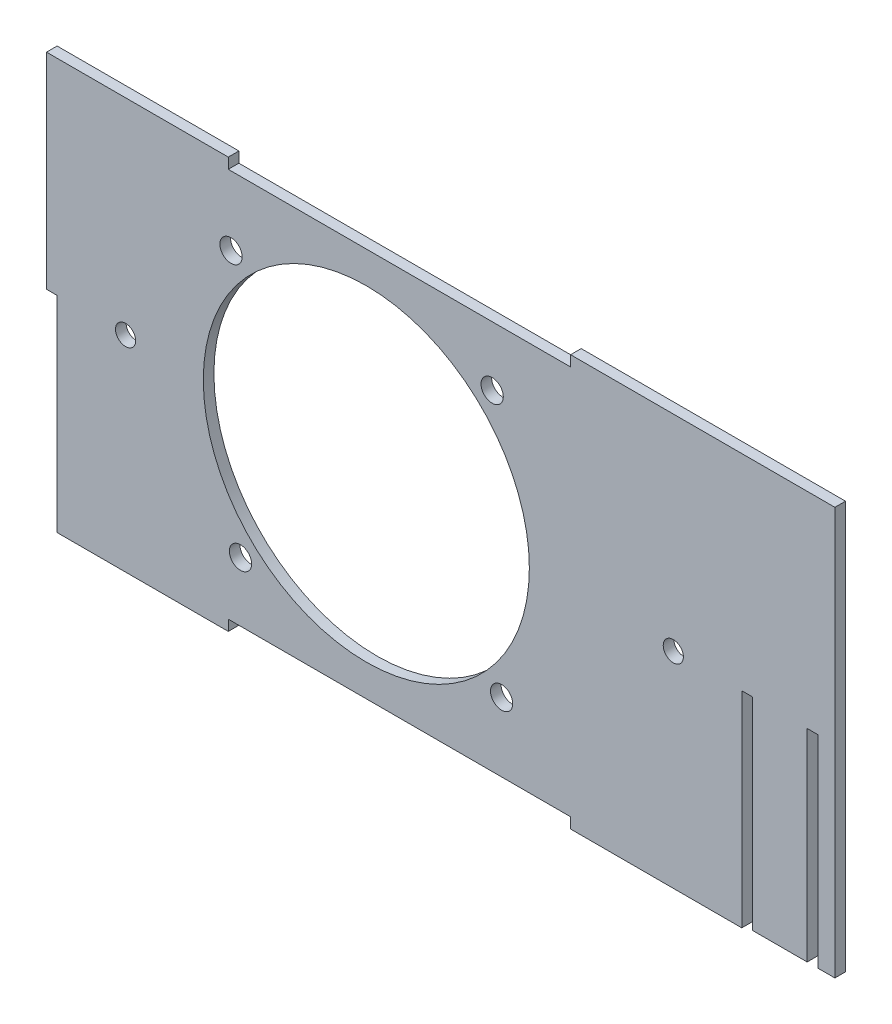
SolidWorks part; units mm, degrees
material "Teak"
ref_plane "Front Plane" through (0, 0, 0) normal (0, 0, 1) x (1, 0, 0)
ref_plane "Top Plane" through (0, 0, 0) normal (0, 1, 0) x (1, 0, 0)
ref_plane "Right Plane" through (0, 0, 0) normal (1, 0, 0) x (0, 0, -1)
sketch "Sketch1" plane through (0, 0, 0) normal (0, 0, 1) x (1, 0, 0)
  line L0 (0, 0) -> (91.2054, 0) construction
  line L1 (9.675, 0) -> (9.675, 60) construction
  line L2 (109.675, -60) -> (-90.325, -60)
  line L3 (109.675, -60) -> (109.675, 60)
  line L4 (109.675, 60) -> (-90.325, 60)
  line L5 (-90.325, -60) -> (-90.325, 60)
  line L6 (109.675, -60) -> (-90.325, 60) construction
  line L7 (109.675, 60) -> (-90.325, -60) construction
  circle A0 centre (-39.5222, 36.76) radius 3.25
  circle A1 centre (36.76, 39.5222) radius 3.25
  circle A2 centre (39.5222, -36.76) radius 3.25
  circle A3 centre (-36.76, -39.5222) radius 3.25
  circle A4 centre (0, 0) radius 47.625
  circle A5 centre (0, 0) radius 60.325 construction
  circle A6 centre (-70.325, 0) radius 2.9456
  circle A7 centre (89.675, 0) radius 2.9456
  point P3 (9.675, 0)
  point P19 (0, 0)
  dimension "D2" = 6.5
  dimension "D3" = 95.25
  dimension "D8" = 120.65
  dimension "D12" = 89.675
  dimension "D4" = 107.95
  dimension "D5" = 0
  dimension "D6" = 120
  dimension "D7" = 20
  dimension "D9" = 200
  dimension "D10" = 70.325
  dimension "D11" = 80
  dimension "D1" = 4
extrude "Boss-Extrude1" add sketch "Sketch1" along normal blind 3.1
sketch "Sketch2" plane through (0, 0, 3.1) normal (0, 0, 1) x (1, 0, 0)
  line L0 (-90.325, 0) -> (-90.325, 60)
  line L1 (-90.325, 0) -> (-93.425, 0)
  line L2 (-90.325, 60) -> (-93.425, 60)
  line L3 (-93.425, 0) -> (-93.425, 60)
  line L4 (-90.325, 60) -> (-90.325, -60) construction
  line L5 (9.675, 60) -> (9.675, -60) construction
  line L6 (109.675, 60) -> (-90.325, 60) construction
  line L7 (-90.325, -60) -> (109.675, -60) construction
  line L8 (112.775, 0) -> (112.775, 60)
  line L9 (109.675, 60) -> (112.775, 60)
  line L10 (109.675, 0) -> (112.775, 0)
  line L11 (109.675, 0) -> (109.675, 60)
  dimension "D1" = 3.1
extrude "Boss-Extrude2" add sketch "Sketch2" against normal through all
sketch "Sketch3" plane through (0, 0, 3.1) normal (0, 0, 1) x (1, 0, 0)
  line L0 (9.675, 60) -> (9.675, -60) construction
  line L1 (112.775, 60) -> (-93.425, 60) construction
  line L2 (-90.325, -60) -> (109.675, -60) construction
  line L3 (0, 0) -> (9.675, 0) construction
  line L4 (-40.325, -56.9) -> (59.675, -56.9)
  line L5 (-40.325, -56.9) -> (-40.325, -60)
  line L6 (-40.325, -60) -> (59.675, -60)
  line L7 (59.675, -56.9) -> (59.675, -60)
  line L8 (-40.325, -56.9) -> (59.675, -60) construction
  line L9 (-40.325, -60) -> (59.675, -56.9) construction
  line L10 (-40.325, 60) -> (59.675, 56.9) construction
  line L11 (-40.325, 56.9) -> (59.675, 60) construction
  line L12 (59.675, 56.9) -> (59.675, 60)
  line L13 (-40.325, 60) -> (59.675, 60)
  line L14 (-40.325, 56.9) -> (-40.325, 60)
  line L15 (-40.325, 56.9) -> (59.675, 56.9)
  point P6 (9.675, -58.45)
  point P18 (9.675, 58.45)
  dimension "D1" = 3.1
  dimension "D2" = 100
extrude "Cut-Extrude1" cut sketch "Sketch3" against normal through all
sketch "Sketch4" plane through (0, 0, 3.1) normal (0, 0, 1) x (1, 0, 0)
  line L0 (112.775, 0) -> (112.775, -59.0807)
  line L1 (112.775, -59.0807) -> (128.775, -59.0807)
  line L2 (128.775, -59.0807) -> (128.775, 0)
  line L3 (128.775, 0) -> (131.875, 0)
  line L4 (131.875, 0) -> (131.875, -59.0807)
  line L5 (131.875, -59.0807) -> (136.875, -59.0807)
  line L6 (136.875, -59.0807) -> (136.875, 60)
  line L7 (136.875, 60) -> (112.775, 60)
  line L24 (-40.325, 56.9) -> (-40.325, 60)
  line L25 (-40.325, 60) -> (-93.425, 60)
  line L26 (-93.425, 60) -> (-93.425, 0)
  line L27 (-93.425, 0) -> (-90.325, 0)
  line L28 (-90.325, 0) -> (-90.325, -60)
  line L29 (-90.325, -60) -> (-40.325, -60)
  line L30 (-40.325, -60) -> (-40.325, -56.9)
  line L31 (-40.325, -56.9) -> (59.675, -56.9)
  line L32 (59.675, -56.9) -> (59.675, -60)
  line L33 (59.675, -60) -> (109.675, -60)
  line L34 (109.675, -60) -> (109.675, 0)
  line L35 (109.675, 0) -> (112.775, 0)
  line L36 (112.775, 0) -> (112.775, 60)
  line L37 (112.775, 60) -> (59.675, 60)
  line L38 (59.675, 60) -> (59.675, 56.9)
  line L39 (59.675, 56.9) -> (-40.325, 56.9)
  line L52 (112.775, 0) -> (112.775, 60)
  dimension "D1" = 3.1
  dimension "D2" = 5
  dimension "D3" = 16
  dimension "D4" = 0
extrude "Boss-Extrude3" add sketch "Sketch4" against normal through all
equation "\"thick\" = 3.1mm"
equation "\"small_bearing_outer\"=12.9mm"
equation "\"servo1_L\"=40.7mm"
equation "\"servo1_W\"=20.5mm"
equation "\"servo1_H\"=43.5mm"
equation "\"servo1_hL\"=49mm"
equation "\"servo1_hW\"=10mm"
equation "\"servo1_H2\"=27mm"
equation "\"large_bearing_inner\"=2.75in"
equation "\"large_bearing_outer\"=4.75in"
equation "\"large_bearing_thick\"=3/8in"
equation "\"large_bearing_h1\"=3.25in"
equation "\"large_bearing_h2\"=4.25in"
equation "\"D3@Sketch1\"=(\"large_bearing_inner\"+\"large_bearing_outer\")/2"
equation "\"D4@Sketch1\"=\"large_bearing_h2\""
equation "\"D8@Sketch1\"=\"large_bearing_outer\""
equation "\"D1@Boss-Extrude1\"=\"thick\""
equation "\"D1@Sketch2\"=\"thick\""
equation "\"D10@Sketch1\"=10 + (\"large_bearing_outer\"/2)"
equation "\"D1@Sketch4\"=\"thick\""
